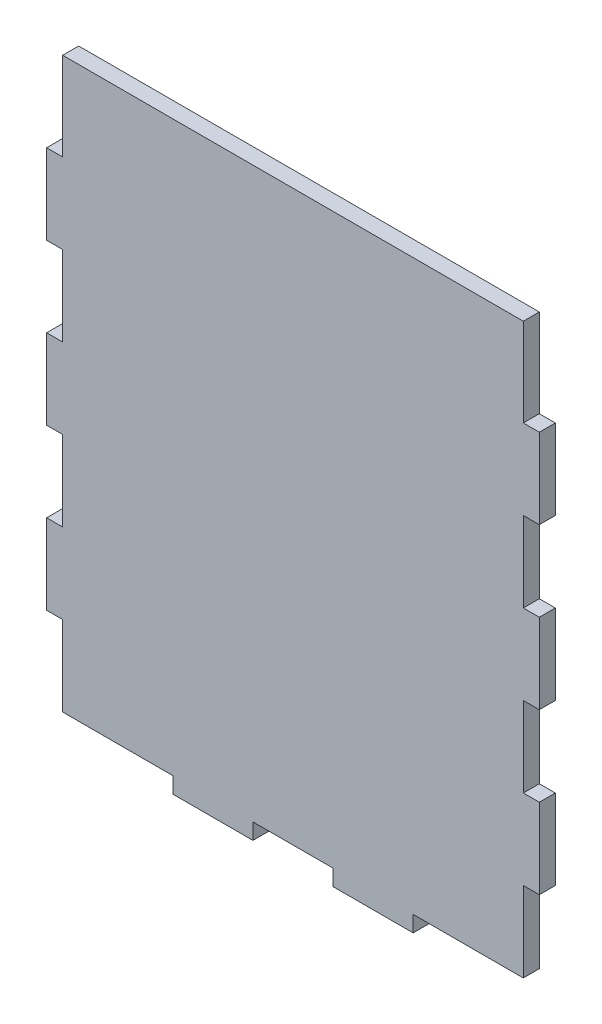
SolidWorks part; units mm, degrees
ref_plane "Спереди" through (0, 0, 0) normal (0, 0, 1) x (1, 0, 0)
ref_plane "Сверху" through (0, 0, 0) normal (0, 1, 0) x (1, 0, 0)
ref_plane "Справа" through (0, 0, 0) normal (1, 0, 0) x (0, 0, -1)
sketch "Эскиз1" plane through (0, 0, 0) normal (0, 0, 1) x (1, 0, 0)
  line L0 (27.5, 0) -> (27.5, -4)
  line L1 (0, 0) -> (27.5, 0)
  line L2 (0, 0) -> (0, 20)
  line L3 (0, 142) -> (115, 142)
  line L4 (115, 0) -> (115, 20)
  line L5 (27.5, -4) -> (47.5, -4)
  line L6 (47.5, -4) -> (47.5, 0)
  line L7 (57.5, 0) -> (57.5, 15.4107) construction
  line L8 (67.5, -4) -> (67.5, 0)
  line L9 (87.5, -4) -> (67.5, -4)
  line L10 (87.5, 0) -> (87.5, -4)
  line L11 (47.5, 0) -> (67.5, 0)
  line L12 (87.5, 0) -> (115, 0)
  line L13 (0, 120) -> (-4, 120)
  line L14 (-4, 120) -> (-4, 100)
  line L15 (-4, 100) -> (0, 100)
  line L16 (0, 80) -> (-4, 80)
  line L17 (-4, 80) -> (-4, 60)
  line L18 (-4, 60) -> (0, 60)
  line L19 (119, 60) -> (115, 60)
  line L20 (119, 80) -> (119, 60)
  line L21 (115, 80) -> (119, 80)
  line L22 (119, 100) -> (115, 100)
  line L23 (119, 120) -> (119, 100)
  line L24 (115, 120) -> (119, 120)
  line L25 (0, 120) -> (0, 142)
  line L26 (0, 80) -> (0, 100)
  line L27 (115, 120) -> (115, 142)
  line L28 (115, 80) -> (115, 100)
  line L29 (0, 40) -> (-4, 40)
  line L30 (-4, 40) -> (-4, 20)
  line L31 (-4, 20) -> (0, 20)
  line L32 (0, 40) -> (0, 60)
  line L33 (119, 20) -> (115, 20)
  line L34 (119, 40) -> (119, 20)
  line L35 (115, 40) -> (119, 40)
  line L36 (115, 40) -> (115, 60)
  dimension "D1" = 115
  dimension "D2" = 142
  dimension "D3" = 4
  dimension "D4" = 20
  dimension "D5" = 20
  dimension "D6" = 20
  dimension "D7" = 20
  dimension "D8" = 4
  dimension "D10" = 20
  dimension "D9" = 3
extrude "Бобышка-Вытянуть1" add sketch "Эскиз1" along normal blind 4
